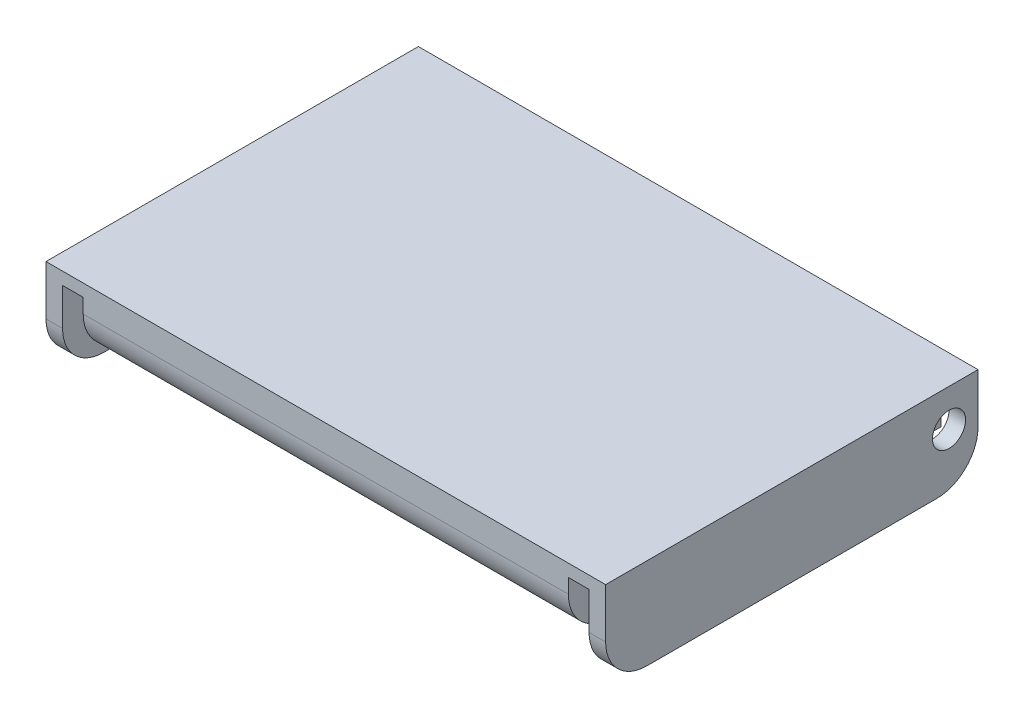
SolidWorks part; units mm, degrees
ref_plane "Front Plane" through (0, 0, 0) normal (0, 0, 1) x (1, 0, 0)
ref_plane "Top Plane" through (0, 0, 0) normal (0, 1, 0) x (1, 0, 0)
ref_plane "Right Plane" through (0, 0, 0) normal (1, 0, 0) x (0, 0, -1)
sketch "Sketch1" plane through (0, 0, 0) normal (0, 1, 0) x (1, 0, 0)
  line L1 (67.625, 45) -> (-67.625, 45)
  line L2 (67.625, 45) -> (67.625, -45)
  line L3 (67.625, -45) -> (-67.625, -45)
  line L4 (-67.625, 45) -> (-67.625, -45)
  line L5 (67.625, 45) -> (-67.625, -45) construction
  line L6 (67.625, -45) -> (-67.625, 45) construction
  point P0 (0, 0)
  dimension "D1" = 135.25
  dimension "D2" = 90
extrude "Boss-Extrude1" add sketch "Sketch1" along normal blind 22
sketch "Sketch4" plane through (0, 0, 45) normal (0, 0, 1) x (1, 0, 0)
  line L0 (-67.625, 0) -> (67.625, 0) construction
  line L1 (-63.625, 19) -> (-58.625, 19)
  line L2 (-63.625, 19) -> (-63.625, 0)
  line L3 (-63.625, 0) -> (-58.625, 0)
  line L4 (-58.625, 19) -> (-58.625, 0)
  line L5 (-63.625, 19) -> (-58.625, 0) construction
  line L6 (-63.625, 0) -> (-58.625, 19) construction
  line L7 (-67.625, 22) -> (-67.625, 0) construction
  line L8 (0, 0) -> (0, 39.0238) construction
  line L9 (63.625, 0) -> (58.625, 0)
  line L10 (58.625, 19) -> (58.625, 0)
  line L11 (63.625, 19) -> (58.625, 19)
  line L12 (63.625, 19) -> (63.625, 0)
  point P0 (-61.125, 9.5)
  dimension "D1" = 5
  dimension "D2" = 4
  dimension "D3" = 19
extrude "Cut-Extrude1" cut sketch "Sketch4" against normal through all
sketch "Sketch5" plane through (0, 0, -45) normal (0, 0, -1) x (-1, 0, 0)
  line L0 (-58.625, 19) -> (-58.625, 0) construction
  line L1 (58.625, -5.5) -> (-58.625, -5.5)
  line L2 (58.625, -5.5) -> (58.625, 5.5)
  line L3 (58.625, 5.5) -> (-58.625, 5.5)
  line L4 (-58.625, -5.5) -> (-58.625, 5.5)
  line L5 (58.625, -5.5) -> (-58.625, 5.5) construction
  line L6 (58.625, 5.5) -> (-58.625, -5.5) construction
  point P0 (0, 0)
  dimension "D1" = 11
extrude "Cut-Extrude2" cut sketch "Sketch5" against normal through all
fillet "Fillet1" radius 10 1 edges at (0, 5.5, 45)
fillet "Fillet2" radius 10 1 edges at (-65.625, 0, 45)
fillet "Fillet3" radius 10 1 edges at (65.625, 0, 45)
fillet "Fillet4" radius 10 1 edges at (-65.625, 0, -45)
fillet "Fillet5" radius 10 1 edges at (65.625, 0, -45)
sketch "Sketch6" plane through (-67.625, 0, 0) normal (-1, 0, 0) x (0, 0, 1)
  line L0 (-45, 22) -> (-45, 10) construction
  line L1 (-45, 22) -> (45, 22) construction
  circle A0 centre (-38, 13) radius 4
  dimension "D1" = 8
  dimension "D2" = 7
  dimension "D3" = 9
extrude "Cut-Extrude3" cut sketch "Sketch6" against normal through all
